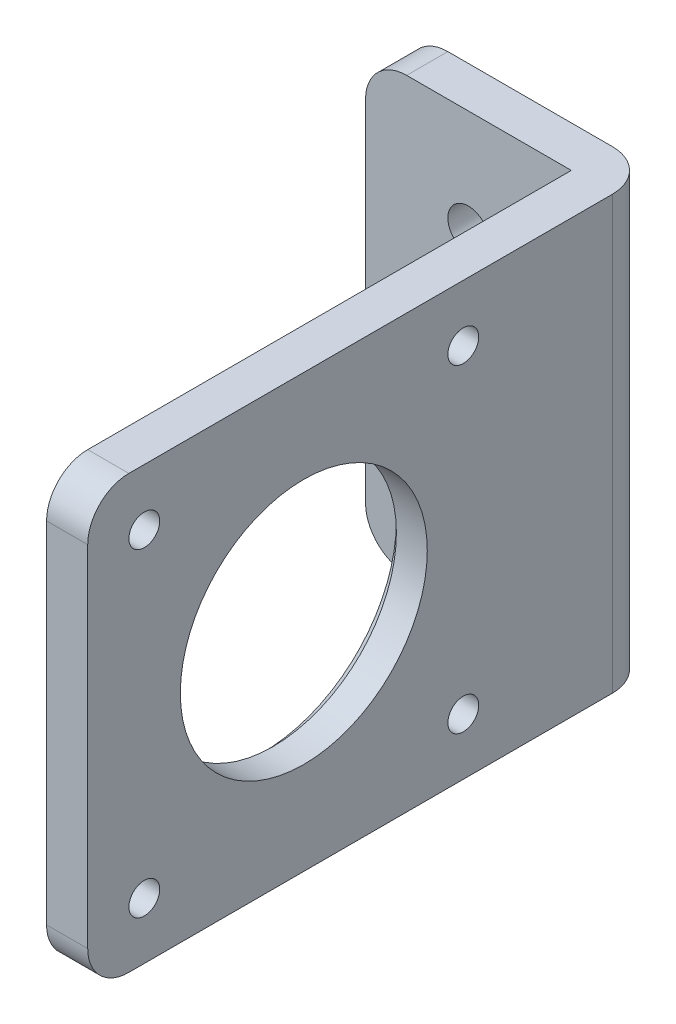
SolidWorks part; units mm, degrees
ref_plane "Front Plane" through (0, 0, 0) normal (0, 0, 1) x (1, 0, 0)
ref_plane "Top Plane" through (0, 0, 0) normal (0, 1, 0) x (1, 0, 0)
ref_plane "Right Plane" through (0, 0, 0) normal (1, 0, 0) x (0, 0, -1)
sketch "Sketch1" plane through (0, 0, 0) normal (0, 1, 0) x (1, 0, 0)
  line L0 (0, 0) -> (0, 51)
  line L1 (0, -55) -> (0, 55) construction
  line L2 (0, 51) -> (-20, 51)
  line L3 (-20, 51) -> (-20, 55)
  line L4 (-20, 55) -> (4, 55)
  line L5 (4, 55) -> (4, 0)
  line L6 (-55, 0) -> (55, 0) construction
  line L7 (4, 0) -> (0, 0)
  dimension "D1" = 4
  dimension "D2" = 55
extrude "Boss-Extrude1" add sketch "Sketch1" along normal blind 42
sketch "Sketch2" plane through (0, 0, 0) normal (-1, 0, 0) x (0, 0, 1)
  line L0 (0, 42) -> (0, 0) construction
  line L7 (-35, 5.5) -> (-36.5, 5.5)
  circle A0 centre (-21, 21) radius 12
  circle A1 centre (-36.5, 5.5) radius 1.5
  circle A2 centre (-5.5, 5.5) radius 1.5
  circle A3 centre (-5.5, 36.5) radius 1.5
  circle A4 centre (-36.5, 36.5) radius 1.5
  point P0 (0, 0)
  point P2 (-11.7624, 8.8131)
  dimension "D1" = 15.5
  dimension "D2" = 24
  dimension "D3" = 21
  dimension "D4" = 15.5
  dimension "D5" = 15.5
  dimension "D6" = 15.5
extrude "Cut-Extrude1" cut sketch "Sketch2" against normal through all contours A0 | A4 | A3 | A2 | A1
sketch "Sketch3" plane through (0, 0, -51) normal (0, 0, 1) x (1, 0, 0)
  line L0 (-10, 0) -> (-10, 42) construction
  line L1 (-20, 0) -> (0, 0) construction
  line L2 (-20, 42) -> (0, 42) construction
  line L3 (-10, 42) -> (-10, 32) construction
  line L4 (-10, 21) -> (-20, 21) construction
  line L5 (-20, 42) -> (-20, 0) construction
  circle A0 centre (-10, 32) radius 2
  circle A1 centre (-10, 10) radius 2
extrude "Cut-Extrude2" cut sketch "Sketch3" against normal through all contours A0 | A1
chamfer "Chamfer2" distance 1 angle 45 1 edges at (0, 21, -9)
fillet "Fillet1" radius 4 5 edges at (4, 21, -55) (2, 0, 0) (2, 42, 0) (-20, 0, -53) (-20, 42, -53)
